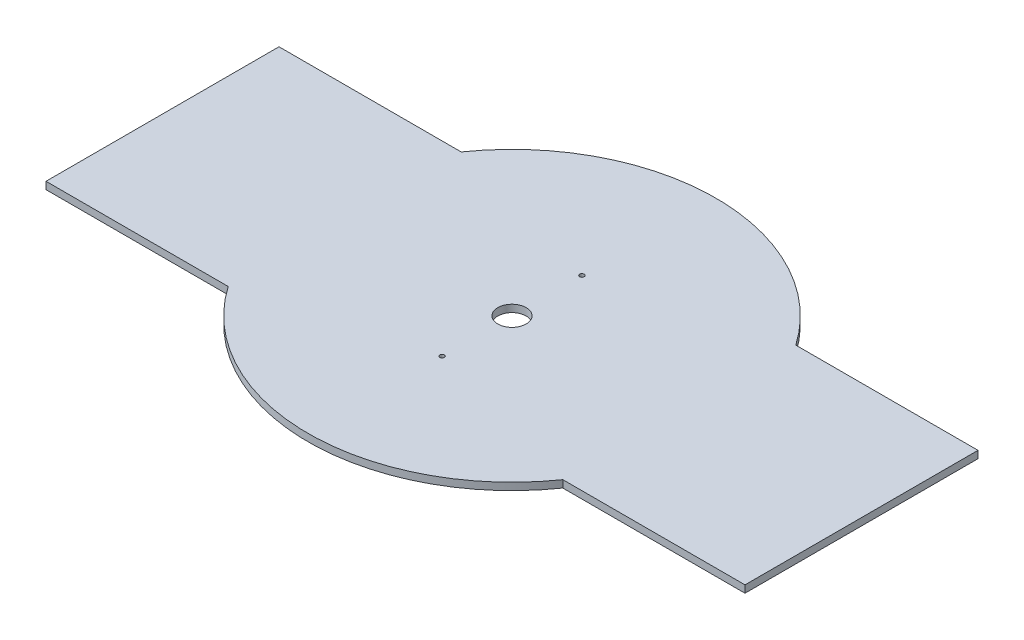
SolidWorks part; units mm, degrees
ref_plane "Front Plane" through (0, 0, 0) normal (0, 0, 1) x (1, 0, 0)
ref_plane "Top Plane" through (0, 0, 0) normal (0, 1, 0) x (1, 0, 0)
ref_plane "Right Plane" through (0, 0, 0) normal (1, 0, 0) x (0, 0, -1)
sketch "Sketch2" plane through (0, 0, 0) normal (0, 1, 0) x (1, 0, 0)
  line L1 (-120, 40) -> (120, 40)
  line L2 (-120, 40) -> (-120, -40)
  line L3 (-120, -40) -> (120, -40)
  line L4 (120, 40) -> (120, -40)
  line L5 (-120, 40) -> (120, -40) construction
  line L6 (-120, -40) -> (120, 40) construction
  circle A0 centre (0, 0) radius 70
  circle A1 centre (0, 0) radius 4.875
  circle A2 centre (0, 24) radius 0.775
  circle A3 centre (0, -24) radius 0.775
  point P12 (0, 0)
  point P13 (0, 0)
  dimension "D1" = 24
  dimension "D2" = 24
  dimension "D3" = 1.55
  dimension "D6" = 9.75
  dimension "D5" = 1.55
  dimension "D4" = 80
extrude "Boss-Extrude1" add sketch "Sketch2" along normal blind 2.5 contours L3 A0 | L3 A0 L1 A1 | L1 A0 | A0 L3 L4 L1 | A0 L1 L2 L3
